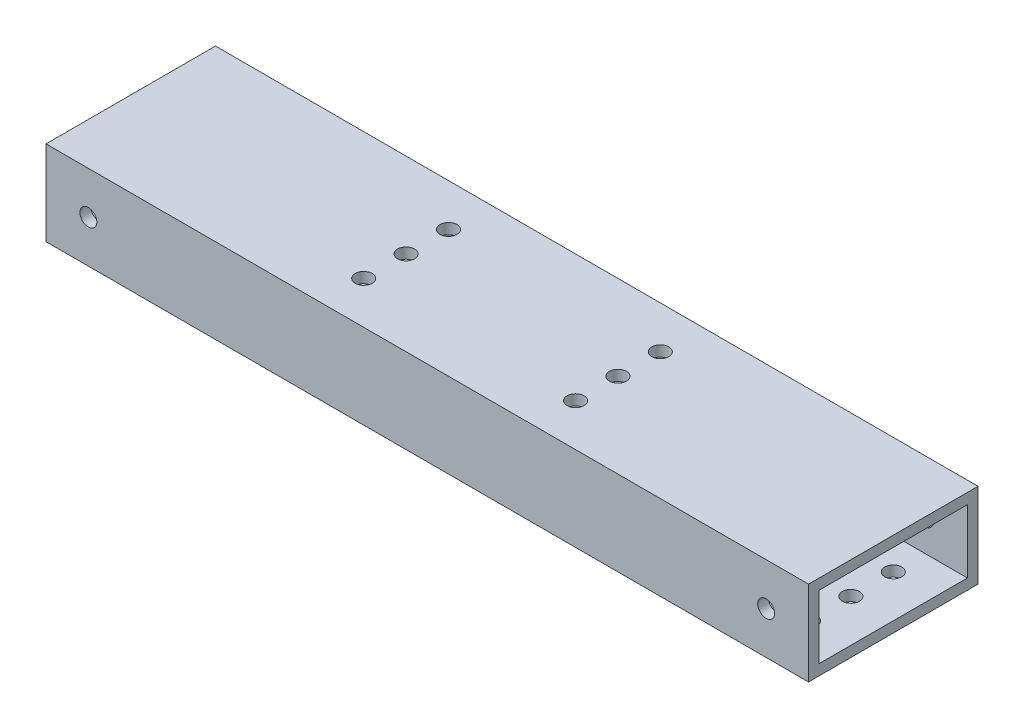
SolidWorks part; units mm, degrees
material "6061-T6 (SS)"
ref_plane "Front" through (0, 0, 0) normal (0, 0, 1) x (1, 0, 0)
ref_plane "Top" through (0, 0, 0) normal (0, 1, 0) x (1, 0, 0)
ref_plane "Right" through (0, 0, 0) normal (1, 0, 0) x (0, 0, -1)
sketch "Sketch1" plane through (0, 0, 0) normal (1, 0, 0) x (0, 0, -1)
  line L1 (-25.4, -12.7) -> (25.4, -12.7)
  line L2 (-25.4, -12.7) -> (-25.4, 12.7)
  line L3 (-25.4, 12.7) -> (25.4, 12.7)
  line L4 (25.4, -12.7) -> (25.4, 12.7)
  line L5 (-25.4, -12.7) -> (25.4, 12.7) construction
  line L6 (-25.4, 12.7) -> (25.4, -12.7) construction
  point P0 (0, 0)
  dimension "D1" = 25.4
  dimension "D2" = 50.8
extrude "Extrude-Thin1" add sketch "Sketch1" along normal blind 228.6 thin thin type one direction reverse wall 3.175
sketch "Sketch4" plane through (0, -12.7, 0) normal (0, -1, 0) x (-1, 0, 0)
  line L0 (-228.6, 25.4) -> (0, 25.4) construction
  line L1 (-228.6, -25.4) -> (0, -25.4) construction
  line L2 (0, -25.4) -> (0, 25.4) construction
  point P36 (-12.7, 15.875)
  point P38 (-38.1, -15.875)
  point P40 (-63.5, 15.875)
  point P52 (-63.5, 15.875)
  point P53 (-88.9, -15.875)
  point P54 (-114.3, 15.875)
  point P55 (-139.7, -15.875)
  point P56 (-165.1, 15.875)
  point P57 (-190.5, -15.875)
  point P58 (-215.9, 15.875)
  point P59 (-241.3, -15.875)
  dimension "D1" = 9.525
  dimension "D2" = 9.525
  dimension "D3" = 50.8
  dimension "D4" = 25.4
  dimension "D6" = 5
  dimension "D5" = 12.7
hole_wizard "1/8 (0.13) Diameter Hole1" positions "Sketch4" profile "Sketch3" hole size "1/8" standard "ANSI Inch"
sketch "Sketch3" plane through (190.5, -12.7, 15.875) normal (1, 0, 0) x (0, 0, -1)
  line L0 (0, 0) -> (0, 3.175)
  line L1 (0, 3.175) -> (1.651, 3.175)
  line L2 (1.651, 3.175) -> (1.651, 0)
  line L5 (1.651, 0) -> (0, 0)
  line L11 (0, -6.35) -> (0, 107.95) construction
  dimension "Thru Hole Dia." = 3.302
  dimension "Thru Hole Depth" = 3.175
sketch "Sketch7" plane through (0, 12.7, 0) normal (0, 1, 0) x (1, 0, 0)
  line L0 (82.55, 12.7) -> (82.55, 0) construction
  line L1 (82.55, 0) -> (82.55, -12.7) construction
  line L4 (114.3, 25.4) -> (114.3, -25.4) construction
  line L5 (228.6, 25.4) -> (0, 25.4) construction
  line L6 (228.6, -25.4) -> (0, -25.4) construction
  line L8 (146.05, 0) -> (146.05, -12.7) construction
  line L9 (146.05, 12.7) -> (146.05, 0) construction
  point P0 (82.55, 12.7)
  point P2 (82.55, 0)
  point P4 (82.55, -12.7)
  point P28 (146.05, -12.7)
  point P29 (146.05, 0)
  point P30 (146.05, 12.7)
  dimension "D1" = 12.7
  dimension "D2" = 31.75
hole_wizard "#10 Clearance Hole1" positions "Sketch7" profile "Sketch6" hole size "#10" standard "ANSI Inch" end condition through all
sketch "Sketch6" plane through (82.55, 12.7, -12.7) normal (1, 0, 0) x (0, 0, 1)
  line L0 (0, 0) -> (0, 25.4)
  line L1 (0, 25.4) -> (2.5527, 25.4)
  line L2 (2.5527, 25.4) -> (2.5527, 0)
  line L5 (2.5527, 0) -> (0, 0)
  line L11 (0, -6.35) -> (0, 107.95) construction
  dimension "Thru Hole Dia." = 5.1054
  dimension "Thru Hole Depth" = 25.4
sketch "Sketch10" plane through (0, 0, 25.4) normal (0, 0, 1) x (1, 0, 0)
  line L0 (228.6, 12.7) -> (0, 12.7) construction
  line L1 (0, 12.7) -> (0, -12.7) construction
  line L2 (228.6, 12.7) -> (228.6, -12.7) construction
  point P0 (12.7, 0)
  point P2 (215.9, 0)
  dimension "D1" = 12.7
  dimension "D2" = 12.7
  dimension "D3" = 12.7
hole_wizard "#10 (0.2) Diameter Hole1" positions "Sketch10" profile "Sketch9" hole size "#10" standard "ANSI Inch" end condition through all
sketch "Sketch9" plane through (12.7, 0, 25.4) normal (1, 0, 0) x (0, -1, 0)
  line L0 (0, 0) -> (0, 50.8)
  line L1 (0, 50.8) -> (2.54, 50.8)
  line L2 (2.54, 50.8) -> (2.54, 0)
  line L5 (2.54, 0) -> (0, 0)
  line L11 (0, -6.35) -> (0, 107.95) construction
  dimension "Thru Hole Dia." = 5.08
  dimension "Thru Hole Depth" = 50.8
sketch "Sketch13" plane through (0, -12.7, 0) normal (0, -1, 0) x (-1, 0, 0)
  line L1 (-215.9, -12.7) -> (-215.9, 0) construction
  line L2 (-215.9, 0) -> (-215.9, 12.7) construction
  line L4 (-228.6, -25.4) -> (-228.6, 25.4) construction
  line L5 (-215.9, 12.7) -> (-215.9, 25.4) construction
  line L6 (-228.6, 25.4) -> (0, 25.4) construction
  line L8 (-215.9, -12.7) -> (-215.9, -25.4) construction
  line L9 (-228.6, -25.4) -> (0, -25.4) construction
  line L11 (-114.3, 25.4) -> (-114.3, -25.4) construction
  line L13 (-12.7, -12.7) -> (-12.7, -25.4) construction
  line L14 (-12.7, 12.7) -> (-12.7, 25.4) construction
  line L15 (-12.7, 0) -> (-12.7, 12.7) construction
  line L16 (-12.7, -12.7) -> (-12.7, 0) construction
  point P0 (-215.9, 12.7)
  point P2 (-215.9, 0)
  point P4 (-215.9, -12.7)
  point P35 (-12.7, -12.7)
  point P36 (-12.7, 0)
  point P37 (-12.7, 12.7)
  dimension "D1" = 12.7
  dimension "D2" = 12.7
hole_wizard "#10 Clearance Hole2" positions "Sketch13" profile "Sketch12" hole size "#10" standard "ANSI Inch" end condition up to next
sketch "Sketch12" plane through (215.9, -12.7, -12.7) normal (1, 0, 0) x (0, 0, -1)
  line L0 (0, 0) -> (0, 3.175)
  line L1 (0, 3.175) -> (2.5527, 3.175)
  line L2 (2.5527, 3.175) -> (2.5527, 0)
  line L5 (2.5527, 0) -> (0, 0)
  line L11 (0, -6.35) -> (0, 107.95) construction
  dimension "Thru Hole Dia." = 5.1054
  dimension "Thru Hole Depth" = 3.175
